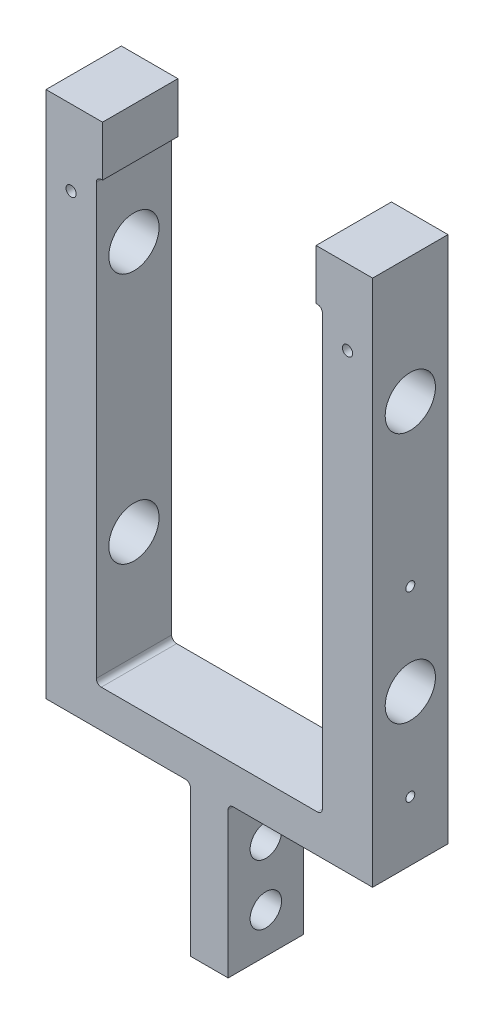
SolidWorks part; units mm, degrees
material "6061 Alloy"
ref_plane "Front Plane" through (0, 0, 0) normal (0, 0, 1) x (1, 0, 0)
ref_plane "Top Plane" through (0, 0, 0) normal (0, 1, 0) x (1, 0, 0)
ref_plane "Right Plane" through (0, 0, 0) normal (1, 0, 0) x (0, 0, -1)
sketch "Sketch1" plane through (0, 0, 0) normal (0, 0, 1) x (1, 0, 0)
  line L7 (9.525, 0) -> (-9.525, 0)
  line L13 (-9.525, 0) -> (-9.525, 19.05)
  line L14 (-9.525, 19.05) -> (-41.275, 19.05)
  line L15 (-41.275, 19.05) -> (-41.275, 131.5967)
  line L17 (-28.575, 139.7) -> (-28.575, 28.575)
  line L18 (-28.575, 28.575) -> (28.575, 28.575)
  line L19 (0, 29.8154) -> (0, -13.1535) construction
  line L20 (28.575, 139.7) -> (28.575, 28.575)
  line L22 (41.275, 19.05) -> (41.275, 131.5967)
  line L23 (9.525, 19.05) -> (41.275, 19.05)
  line L24 (9.525, 0) -> (9.525, 19.05)
  line L25 (41.275, 131.5967) -> (41.275, 152.4)
  line L26 (41.275, 152.4) -> (-41.275, 152.4)
  line L27 (-41.275, 152.4) -> (-41.275, 131.5967)
  line L29 (28.575, 139.7) -> (-28.575, 139.7)
  point P12 (0, 28.575)
  point P17 (0, 0)
  dimension "D1" = 19.05
  dimension "D2" = 57.15
  dimension "D3" = 19.05
  dimension "D4" = 82.55
  dimension "D5" = 111.125
  dimension "D6" = 12.7
  dimension "D7" = 152.4
extrude "Boss-Extrude1" add sketch "Sketch1" along normal mid plane 19.05
sketch "Sketch2" plane through (-41.275, 0, 0) normal (-1, 0, 0) x (0, 0, 1)
  line L0 (-26.0251, 0) -> (40.3307, 0) construction
  line L1 (0, 127) -> (0, 0) construction
  circle A0 centre (0, 57.15) radius 6.35
  circle A1 centre (0, 120.65) radius 6.35
  dimension "D2" = 12.7
  dimension "D1" = 12.7
  dimension "D4" = 63.5
  dimension "D3" = 57.15
extrude "Cut-Extrude1" cut sketch "Sketch2" against normal through all
sketch "Sketch4" plane through (0, 0, -9.525) normal (0, 0, -1) x (-1, 0, 0)
  line L1 (9.525, 0) -> (-9.525, 0) construction
  line L2 (9.525, 0) -> (9.525, 19.05) construction
  line L3 (9.525, 19.05) -> (-9.525, 19.05) construction
  line L4 (-9.525, 0) -> (-9.525, 19.05) construction
  line L5 (-4.7625, 19.0579) -> (4.7625, 19.0579) construction
  line L6 (-4.7625, 19.0579) -> (-4.7625, 0) construction
  line L7 (-4.7625, 0) -> (4.7625, 0) construction
  line L8 (4.7625, 19.0579) -> (4.7625, 0) construction
  line L9 (-4.7625, 19.0579) -> (4.7625, 0) construction
  line L10 (-4.7625, 0) -> (4.7625, 19.0579) construction
  line L11 (-9.525, 19.05) -> (-4.7625, 19.05)
  line L12 (-9.525, 19.05) -> (-9.525, 0)
  line L13 (-9.525, 0) -> (-4.7625, 0)
  line L14 (-4.7625, 19.05) -> (-4.7625, 0)
  line L15 (4.7625, 19.0579) -> (9.525, 19.0579)
  line L16 (4.7625, 19.0579) -> (4.7625, 0)
  line L17 (4.7625, 0) -> (9.525, 0)
  line L18 (9.525, 19.0579) -> (9.525, 0)
  point P6 (0, 9.529)
  dimension "D1" = 9.525
extrude "Cut-Extrude2" cut sketch "Sketch4" against normal through all
sketch "Sketch5" plane through (-4.7625, 0, 0) normal (-1, 0, 0) x (0, 0, 1)
  circle A0 centre (0, 6.35) radius 4.7625
  dimension "D1" = 9.525
  dimension "D2" = 6.35
sketch "Sketch6" plane through (41.275, 0, 0) normal (-1, 0, 0) x (0, 0, 1)
  line L0 (0, 80.1624) -> (0, 34.1376) construction
  point P5 (0, 57.15)
  dimension "D1" = 46.0248
hole_wizard "#4-40 Tapped Hole2" positions "Sketch12" profile "Sketch13" tap size "#4-40" standard "ANSI Inch"
sketch "Sketch12" plane through (41.275, 0, 0) normal (1, 0, 0) x (0, 0, -1)
  point P0 (0, 80.1624)
  point P3 (0, 34.1376)
sketch "Sketch13" plane through (41.275, 80.1624, 0) normal (0, 1, 0) x (0, 0, -1)
  line L0 (0, 0) -> (0, 13.3792)
  line L1 (0, 13.3792) -> (1.1303, 12.7)
  line L2 (1.1303, 12.7) -> (1.1303, 0)
  line L5 (1.1303, 0) -> (0, 0)
  line L10 (0, 13.3792) -> (-1.1303, 12.7) construction
  line L11 (0, -6.35) -> (0, 107.95) construction
  dimension "Tap Drill Dia." = 2.2606
  dimension "Tap Drill Depth" = 12.7
  dimension "Drill Angle" = 118
cosmetic thread "Hole Thread5" parameters "D1"=82.55, "D2"=2.8448
cosmetic thread "Hole Thread6" parameters "D1"=82.55, "D2"=2.8448
sketch "Sketch14" plane through (0, 0, 0) normal (0, -1, 0) x (1, 0, 0)
  line L1 (4.7625, -9.525) -> (-4.7625, -9.525)
  line L2 (4.7625, -9.525) -> (4.7625, 9.525)
  line L3 (4.7625, 9.525) -> (-4.7625, 9.525)
  line L4 (-4.7625, -9.525) -> (-4.7625, 9.525)
extrude "Boss-Extrude2" add sketch "Sketch14" along normal blind 19.05
hole_wizard "Hole1" positions "Sketch15" profile "Sketch16" legacy end condition through all
sketch "Sketch15" plane through (-4.7625, 0, 0) normal (-1, 0, 0) x (0, 0, 1)
  point P0 (0, 6.35)
  point P3 (0, -8.89)
  dimension "D1" = 8.89
sketch "Sketch16" plane through (-4.7625, 6.35, 0) normal (0, 1, 0) x (0, 0, 1)
  line L0 (0, 0) -> (0, 48.4245)
  line L1 (0, 48.4245) -> (3.9726, 46.0375)
  line L2 (3.9726, 46.0375) -> (3.9726, 0)
  line L4 (3.9726, 0) -> (0, 0)
  line L6 (0, 48.4245) -> (-3.9726, 46.0375) construction
  line L7 (0, -4.2442) -> (0, 117.3081) construction
  dimension "Diameter" = 7.9451
  dimension "Depth" = 46.0375
  dimension "Drill Angle" = 118
fillet "Fillet1" radius 1.27 6 edges at (4.7625, 19.05, 0) (-4.7625, 19.0579, 0) (-28.575, 28.575, 0) (28.575, 28.575, 0) (28.575, 139.7, 0) (-28.575, 139.7, 0)
sketch "Sketch17" plane through (0, 0, 9.525) normal (0, 0, 1) x (1, 0, 0)
  line L0 (0, 152.4) -> (0, 117.2896) construction
  line L1 (41.275, 152.4) -> (-41.275, 152.4) construction
  line L2 (23.5336, 152.4) -> (23.5336, 139.7) construction
  line L3 (27.305, 139.7) -> (-27.305, 139.7) construction
  line L4 (23.5336, 146.05) -> (-38.274, 146.05) construction
  line L6 (-26.9875, 152.4) -> (26.9875, 152.4)
  line L7 (-26.9875, 152.4) -> (-26.9875, 139.7)
  line L8 (-26.9875, 139.7) -> (26.9875, 139.7)
  line L9 (26.9875, 152.4) -> (26.9875, 139.7)
  line L10 (-26.9875, 152.4) -> (26.9875, 139.7) construction
  line L11 (-26.9875, 139.7) -> (26.9875, 152.4) construction
  point P11 (0, 146.05)
  point P12 (0, 146.05)
  dimension "D1" = 53.975
extrude "Cut-Extrude3" cut sketch "Sketch17" against normal through all
hole_wizard "#5-40 Tapped Hole1" positions "Sketch18" profile "Sketch19" tap size "#5-40" standard "ANSI Inch" end condition through all
sketch "Sketch18" plane through (0, 0, 9.525) normal (0, 0, 1) x (1, 0, 0)
  line L4 (-41.275, 133.35) -> (-28.575, 133.35) construction
  line L5 (-41.275, 152.4) -> (-41.275, 19.05) construction
  line L6 (-28.575, 138.43) -> (-28.575, 29.845) construction
  line L7 (-26.9875, 152.4) -> (-41.275, 152.4) construction
  line L8 (28.575, 133.35) -> (41.275, 133.35) construction
  line L9 (28.575, 29.845) -> (28.575, 138.43) construction
  line L10 (41.275, 19.05) -> (41.275, 152.4) construction
  point P18 (-34.925, 133.35)
  point P31 (34.925, 133.35)
  dimension "D1" = 19.05
sketch "Sketch19" plane through (34.925, 133.35, 9.525) normal (1, 0, 0) x (0, -1, 0)
  line L0 (0, 0) -> (0, 19.05)
  line L1 (0, 19.05) -> (1.289, 19.05)
  line L2 (1.289, 19.05) -> (1.289, 0)
  line L5 (1.289, 0) -> (0, 0)
  line L11 (0, -6.35) -> (0, 107.95) construction
  dimension "Thru Tap Drill Dia." = 2.5781
  dimension "Thru Tap Drill Depth" = 19.05
cosmetic thread "Hole Thread7" parameters "D2"=3.175
cosmetic thread "Hole Thread8" parameters "D2"=3.175
equation "\"BoomDistance\"=2.5"
equation "\"D4@Sketch2\"=\"BoomDistance\""
